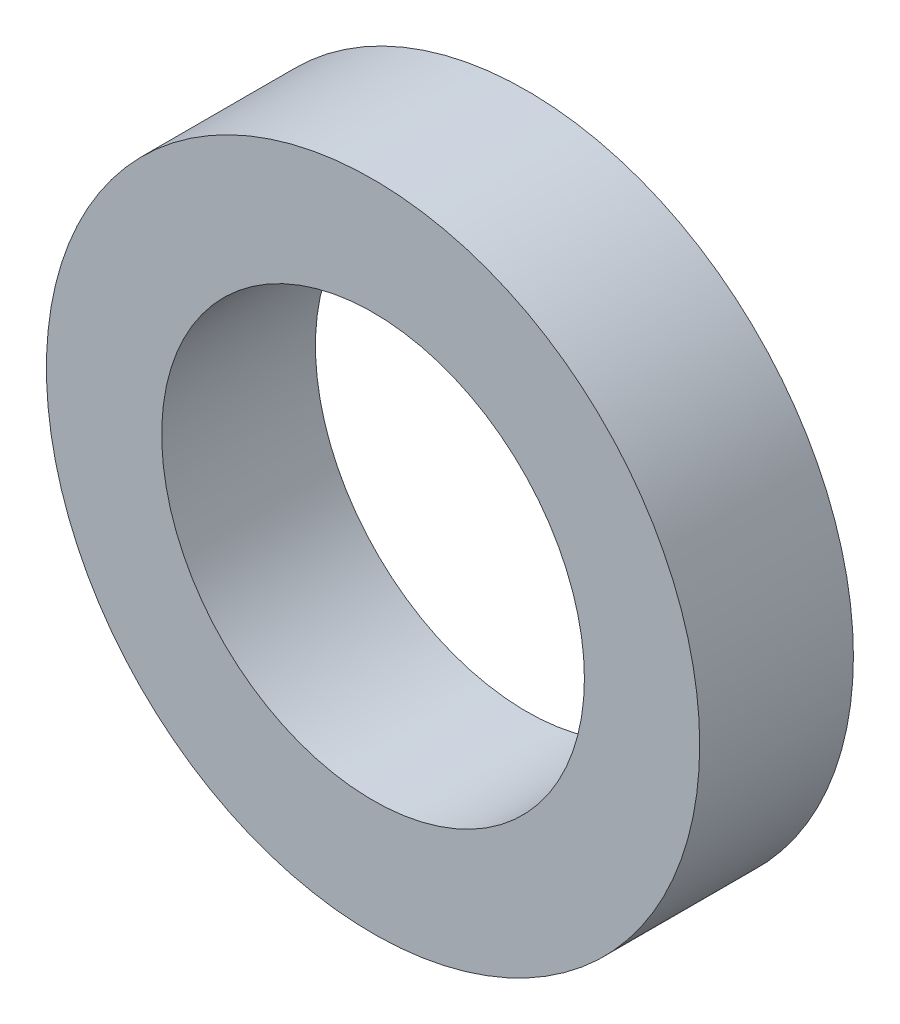
SolidWorks part; units mm, degrees
ref_plane "Front" through (0, 0, 0) normal (0, 0, 1) x (1, 0, 0)
ref_plane "Top" through (0, 0, 0) normal (0, 1, 0) x (1, 0, 0)
ref_plane "Right" through (0, 0, 0) normal (1, 0, 0) x (0, 0, -1)
sketch "Sketch1" plane through (0, 0, 0) normal (0, 0, 1) x (1, 0, 0)
  circle A0 centre (0, 0) radius 2.75
  circle A1 centre (0, 0) radius 4.25
  dimension "D2" = 5.5
  dimension "D1" = 1.5
extrude "Boss-Extrude1" add sketch "Sketch1" along normal blind 2
